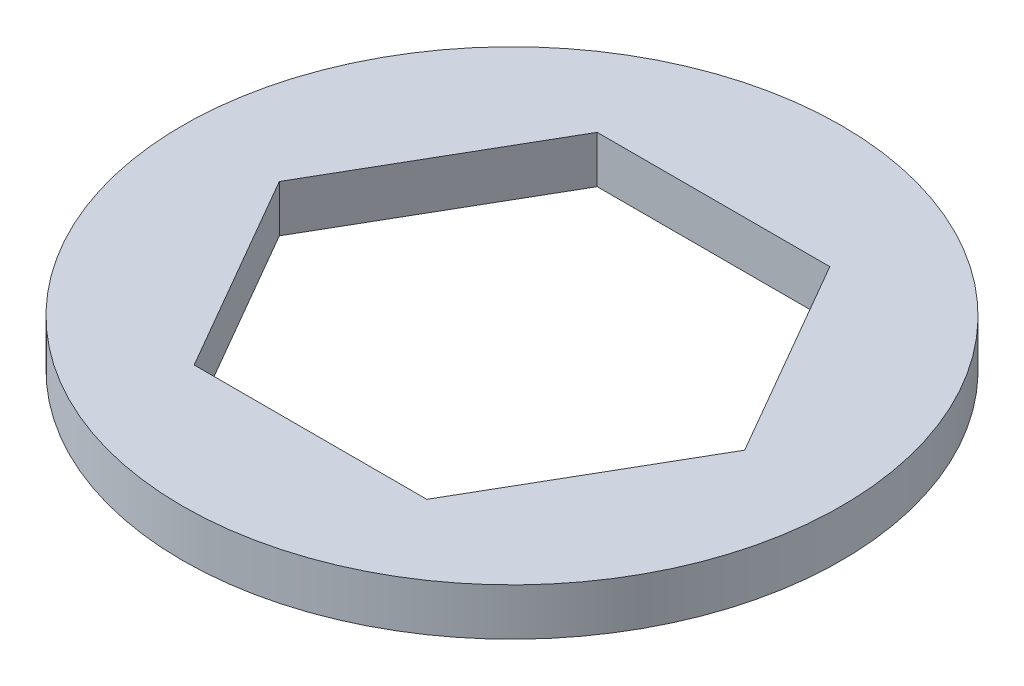
SolidWorks part; units mm, degrees
ref_plane "Front" through (0, 0, 0) normal (0, 0, 1) x (1, 0, 0)
ref_plane "Top" through (0, 0, 0) normal (0, 1, 0) x (1, 0, 0)
ref_plane "Right" through (0, 0, 0) normal (1, 0, 0) x (0, 0, -1)
sketch "Sketch1" plane through (0, 0, 0) normal (0, 1, 0) x (1, 0, 0)
  line L1 (7.8456, 0) -> (3.9228, 6.7945)
  line L2 (3.9228, 6.7945) -> (-3.9228, 6.7945)
  line L3 (-3.9228, 6.7945) -> (-7.8456, 0)
  line L4 (-7.8456, 0) -> (-3.9228, -6.7945)
  line L5 (-3.9228, -6.7945) -> (3.9228, -6.7945)
  line L6 (3.9228, -6.7945) -> (7.8456, 0)
  circle A0 centre (0, 0) radius 6.7945 construction
  circle A1 centre (0, 0) radius 11.1125
  dimension "D1" = 22.225
extrude "Boss-Extrude1" add sketch "Sketch1" along normal blind 1.5875
